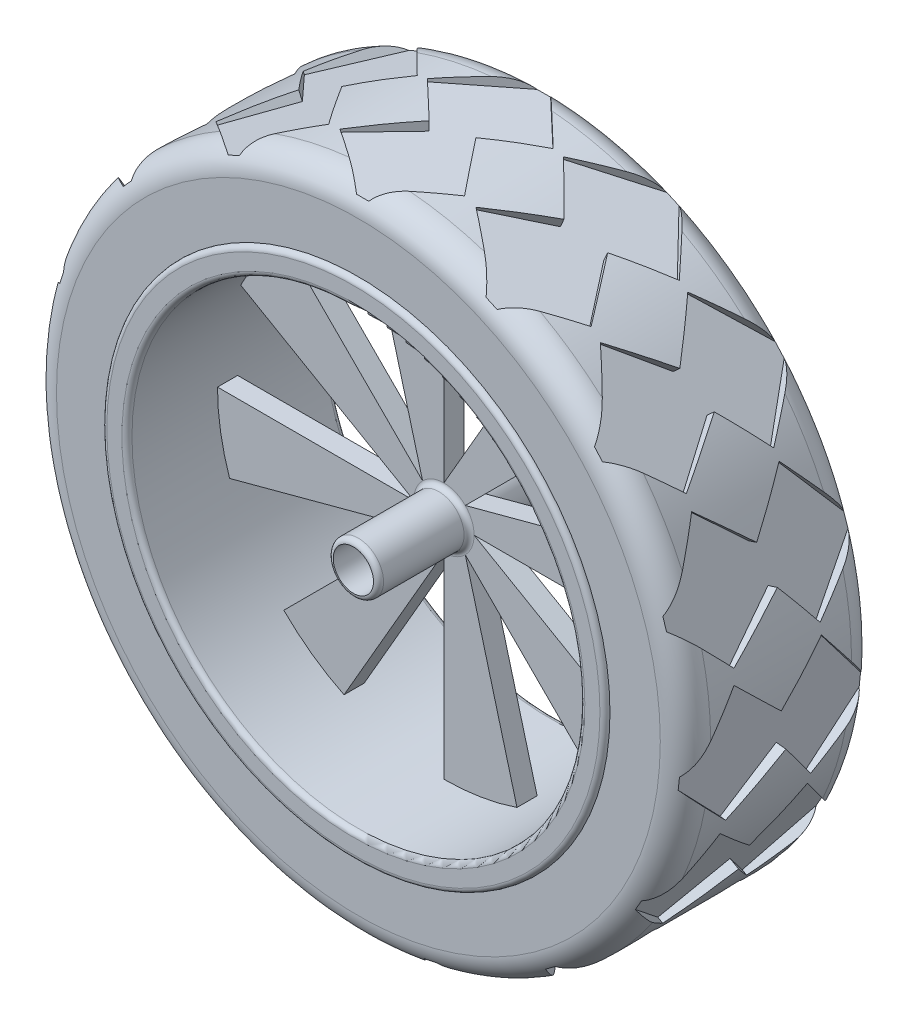
SolidWorks part; units mm, degrees
ref_plane "Alzado" through (0, 0, 0) normal (0, 0, 1) x (1, 0, 0)
ref_plane "Planta" through (0, 0, 0) normal (0, 1, 0) x (1, 0, 0)
ref_plane "Vista lateral" through (0, 0, 0) normal (1, 0, 0) x (0, 0, -1)
sketch "Croquis1" plane through (0, 0, 0) normal (1, 0, 0) x (0, 0, -1)
  line L0 (0, 0) -> (-19, 0)
  line L1 (-20, 1) -> (-20, 4)
  line L2 (-19, 5) -> (-3, 5)
  line L3 (-2, 6) -> (-2, 45)
  line L4 (-2, 45) -> (-19, 45)
  line L5 (-20, 46) -> (-20, 49)
  line L6 (-19, 50) -> (19, 50)
  line L7 (0, 0) -> (19, 0)
  line L8 (20, 1) -> (20, 4)
  line L9 (19, 5) -> (3, 5)
  line L10 (2, 6) -> (2, 45)
  line L11 (2, 45) -> (19, 45)
  line L12 (20, 46) -> (20, 49)
  arc A0 (3, 5) -> (2, 6) centre (3, 6) cw
  arc A1 (-3, 5) -> (-2, 6) centre (-3, 6) ccw
  arc A2 (19, 0) -> (20, 1) centre (19, 1) ccw
  arc A3 (20, 4) -> (19, 5) centre (19, 4) ccw
  arc A4 (-19, 0) -> (-20, 1) centre (-19, 1) cw
  arc A5 (-20, 4) -> (-19, 5) centre (-19, 4) cw
  arc A6 (19, 45) -> (20, 46) centre (19, 46) ccw
  arc A7 (19, 50) -> (20, 49) centre (19, 49) cw
  arc A8 (-19, 45) -> (-20, 46) centre (-19, 46) cw
  arc A9 (-20, 49) -> (-19, 50) centre (-19, 49) cw
  point P16 (2, 5)
  point P19 (-2, 5)
  point P22 (20, 0)
  point P25 (20, 5)
  point P28 (-20, 0)
  point P31 (-20, 5)
  point P38 (-20, 45)
  point P41 (-20, 50)
  point P42 (9.5, 0)
  dimension "D7" = 1
  dimension "D1" = 20
  dimension "D2" = 5
  dimension "5" = 5
  dimension "D3" = 18
  dimension "D4" = 18
  dimension "D5" = 20
  dimension "D6" = 18
  dimension "D8" = 50
revolve "Revolución1" add sketch "Croquis1" angle 360 about L7
sketch "Croquis2" plane through (0, 0, 20) normal (0, 0, 1) x (1, 0, 0)
  circle A0 centre (0, 0) radius 4
  dimension "D1" = 8
extrude "Cortar-Extruir1" cut sketch "Croquis2" against normal through all
sketch "Croquis3" plane through (0, 0, 2) normal (0, 0, 1) x (1, 0, 0)
  line L0 (0, 0) -> (0, 45) construction
  line L1 (0, 6) -> (0, 45)
  line L2 (0, 6) -> (19.8519, 40.3844)
  line L3 (4.2426, 4.2426) -> (42.5935, 14.5187)
  line L4 (4.2426, 4.2426) -> (31.8198, 31.8198)
  line L5 (6, 0) -> (40.3844, -19.8519)
  line L6 (6, 0) -> (45, 0)
  line L7 (4.2426, -4.2426) -> (14.5187, -42.5935)
  line L8 (4.2426, -4.2426) -> (31.8198, -31.8198)
  line L9 (0, -6) -> (-19.8519, -40.3844)
  line L10 (0, -6) -> (0, -45)
  line L11 (-4.2426, -4.2426) -> (-42.5935, -14.5187)
  line L12 (-4.2426, -4.2426) -> (-31.8198, -31.8198)
  line L13 (-6, 0) -> (-40.3844, 19.8519)
  line L14 (-6, 0) -> (-45, 0)
  line L15 (-4.2426, 4.2426) -> (-14.5187, 42.5935)
  line L16 (-4.2426, 4.2426) -> (-31.8198, 31.8198)
  circle A0 centre (0, 0) radius 45 construction
  circle A1 centre (0, 0) radius 6 construction
  arc A15 (0, 45) -> (19.8519, 40.3844) centre (0, 0) cw
  arc A16 (31.8198, 31.8198) -> (42.5935, 14.5187) centre (0, 0) cw
  arc A17 (45, 0) -> (40.3844, -19.8519) centre (0, 0) cw
  arc A18 (31.8198, -31.8198) -> (14.5187, -42.5935) centre (0, 0) cw
  arc A19 (0, -45) -> (-19.8519, -40.3844) centre (0, 0) cw
  arc A20 (-31.8198, -31.8198) -> (-42.5935, -14.5187) centre (0, 0) cw
  arc A21 (-45, 0) -> (-40.3844, 19.8519) centre (0, 0) cw
  arc A22 (-31.8198, 31.8198) -> (-14.5187, 42.5935) centre (0, 0) cw
  point P28 (4.2013, 18.0701)
  point P35 (0, 0)
  point P42 (0, 0)
  dimension "D1" = 30
  dimension "D2" = 8
extrude "Cortar-Extruir2" cut sketch "Croquis3" against normal through all
ref_plane "Plano1" through (0, 0, 0) normal (1, 0, 0) x (0, 0, -1)
sketch "Croquis4" plane through (0, 0, 0) normal (1, 0, 0) x (0, 0, -1)
  line L0 (-19, 50) -> (19, 50)
  line L1 (-19, 50) -> (-19, -50) construction
  line L2 (19, 50) -> (19, 60)
  line L3 (14, 65) -> (-14, 65)
  line L4 (-19, 60) -> (-19, 50)
  line L5 (0, 0) -> (20, 0) construction
  line L6 (20, -49) -> (20, 49) construction
  line L7 (20, 0) -> (-20, 0) construction
  line L8 (-20, 49) -> (-20, -49) construction
  arc A0 (-19, 50) -> (-20, 49) centre (-19, 49) ccw construction
  arc A1 (19, 60) -> (14, 65) centre (14, 60) ccw
  arc A2 (-14, 65) -> (-19, 60) centre (-14, 60) ccw
  point P14 (-19, 65)
  dimension "D2" = 5
  dimension "D1" = 15
revolve "Revolución2" add sketch "Croquis4" angle 360 about L7
ref_plane "Plano2" through (0, 65, 0) normal (0, 1, 0) x (1, 0, 0)
sketch "Croquis5" plane through (0, 65, 0) normal (0, 1, 0) x (1, 0, 0)
  line L0 (0, 19.1326) -> (0, -19) construction
  line L1 (-50, -19) -> (50, -19) construction
  line L2 (0, -19) -> (-13.6799, -8.9844)
  line L3 (-13.6799, -8.9844) -> (-5.0018, 0.0663)
  line L4 (-5.0018, 0.0663) -> (-13.6799, 8.3871)
  line L5 (0, 19.1326) -> (-13.6799, 8.3871)
  line L7 (0, 19.1326) -> (11.3289, 8.3871)
  line L8 (11.3289, 8.3871) -> (2.7032, 1.6535)
  line L9 (2.7032, 1.6535) -> (10.7565, -8.6628)
  line L10 (10.7565, -8.6628) -> (0, -19)
  point P4 (11.3289, -8.1127)
  point P11 (2.7032, 1.6535)
extrude "Cortar-Extruir3" cut sketch "Croquis5" against normal blind 2
pattern_circular "MatrizC1" count 15 over 360 about axis through (0, 0, 0) along (0, 0, 1) of "Cortar-Extruir3"
